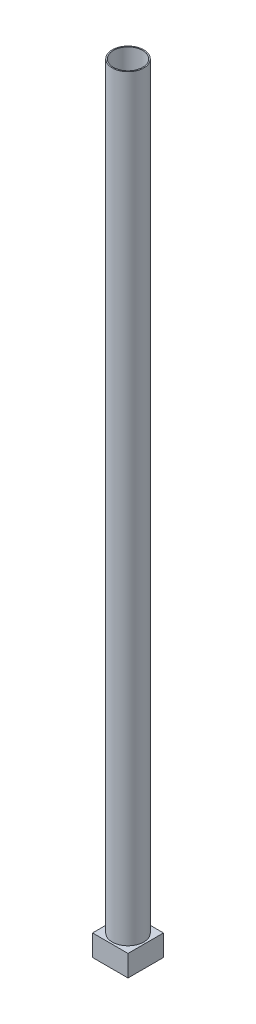
SolidWorks part; units mm, degrees
ref_plane "Front Plane" through (0, 0, 0) normal (0, 0, 1) x (1, 0, 0)
ref_plane "Top Plane" through (0, 0, 0) normal (0, 1, 0) x (1, 0, 0)
ref_plane "Right Plane" through (0, 0, 0) normal (1, 0, 0) x (0, 0, -1)
sketch "Sketch1" plane through (0, 0, 0) normal (0, 1, 0) x (1, 0, 0)
  line L1 (-50, 50) -> (50, 50)
  line L2 (-50, 50) -> (-50, -50)
  line L3 (-50, -50) -> (50, -50)
  line L4 (50, 50) -> (50, -50)
  line L5 (-50, 50) -> (50, -50) construction
  line L6 (-50, -50) -> (50, 50) construction
  point P0 (0, 0)
  dimension "D1" = 100
extrude "Boss-Extrude1" add sketch "Sketch1" along normal mid plane 60
sketch "Sketch2" plane through (0, 30, 0) normal (0, 1, 0) x (1, 0, 0)
  circle A0 centre (0, 0) radius 44.45
  circle A1 centre (0, 0) radius 41.275
  dimension "D1" = 88.9
  dimension "D2" = 3.175
extrude "Boss-Extrude2" add sketch "Sketch2" along normal blind 2133.6
